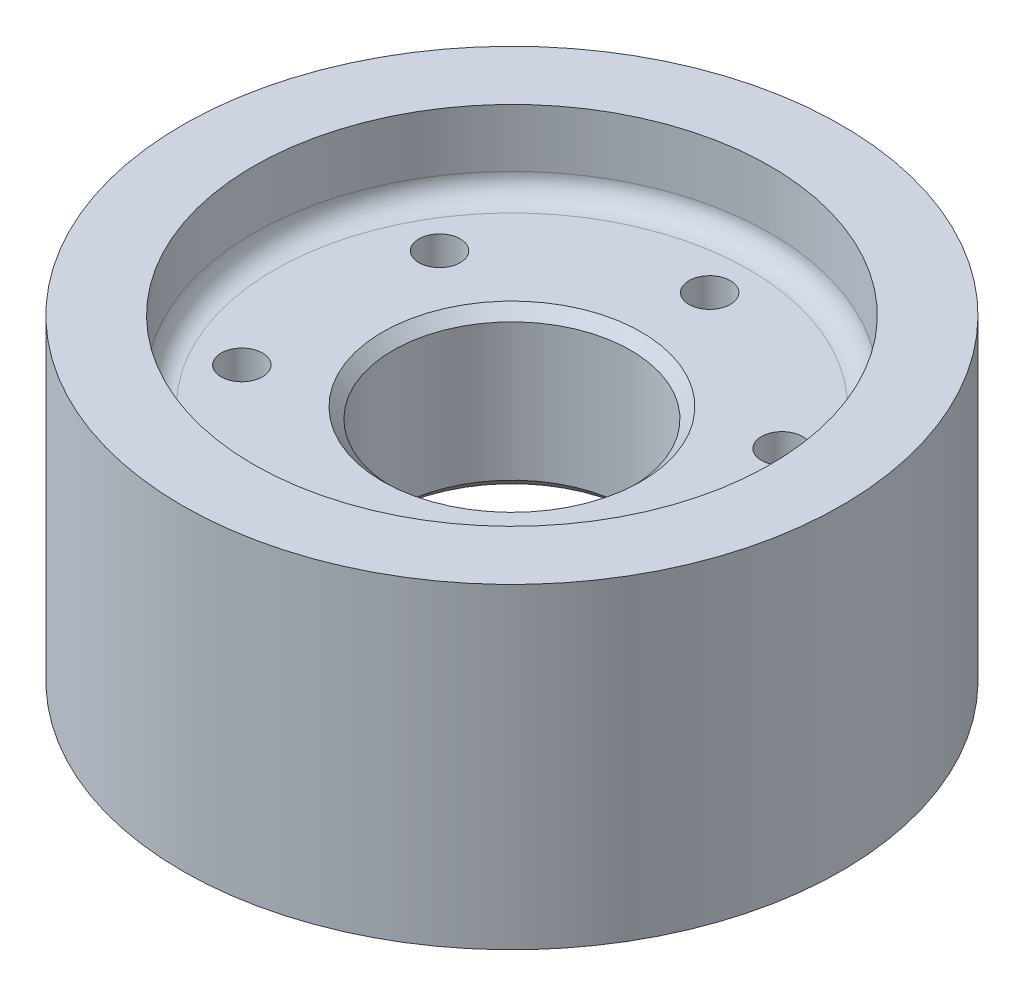
SolidWorks part; units mm, degrees
material "AISI 4130 Steel, normalized at 870C"
ref_plane "Front Plane" through (0, 0, 0) normal (0, 0, 1) x (1, 0, 0)
ref_plane "Top Plane" through (0, 0, 0) normal (0, 1, 0) x (1, 0, 0)
ref_plane "Right Plane" through (0, 0, 0) normal (1, 0, 0) x (0, 0, -1)
sketch "Sketch1" plane through (0, 0, 0) normal (0, 1, 0) x (1, 0, 0)
  circle A0 centre (0, 0) radius 38.1
  circle A1 centre (0, 0) radius 14.3129
  dimension "D1" = 28.6258
  dimension "D2" = 76.2
extrude "Boss-Extrude1" add sketch "Sketch1" along normal mid plane 19.05
sketch "Sketch2" plane through (0, 0, 0) normal (0, 1, 0) x (1, 0, 0)
  circle A0 centre (0, 0) radius 39.6875
  circle A1 centre (0, 0) radius 31.115
  dimension "D1" = 79.375
  dimension "D2" = 62.23
extrude "Boss-Extrude2" add sketch "Sketch2" along normal mid plane 38.1
hole_wizard "#10 Clearance Hole1" positions "Sketch5" profile "Sketch6" hole size "#10" standard "ANSI Inch" end condition through all
sketch "Sketch5" plane through (0, 9.525, 0) normal (0, 1, 0) x (1, 0, 0)
  circle A0 centre (0, 0) radius 23.8125 construction
  point P5 (0, 23.8125)
  dimension "D1" = 47.625
sketch "Sketch6" plane through (0, 9.525, -23.8125) normal (1, 0, 0) x (0, 0, 1)
  line L0 (0, 0) -> (0, 28.575)
  line L1 (0, 28.575) -> (2.4892, 28.575)
  line L2 (2.4892, 28.575) -> (2.4892, 0)
  line L5 (2.4892, 0) -> (0, 0)
  line L11 (0, -6.35) -> (0, 107.95) construction
  dimension "Thru Hole Dia." = 4.9784
  dimension "Thru Hole Depth" = 28.575
pattern_circular "CirPattern1" count 6 over 360 about axis through (0, 0, 0) along (0, 1, 0) of "#10 Clearance Hole1"
chamfer "Chamfer1" distance 1.27 angle 45 2 edges at (0, 9.525, 14.3129) (0, -9.525, 14.3129)
fillet "Fillet2" radius 2.54 2 edges at (0, -9.525, 31.115) (0, 9.525, 31.115)
